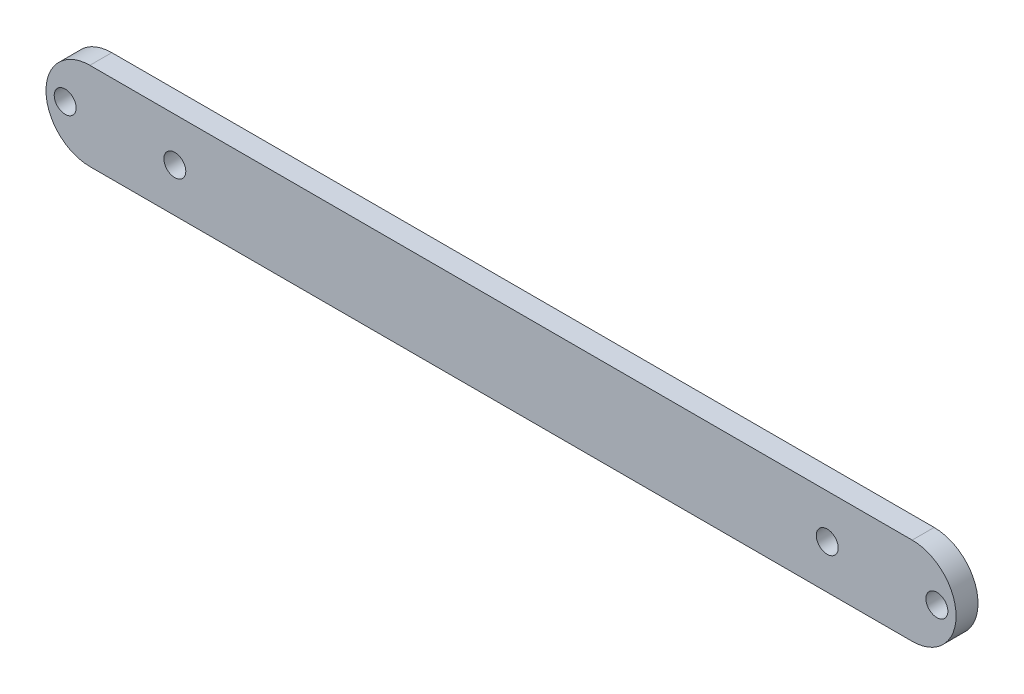
SolidWorks part; units mm, degrees
material "Thornel Mat VMA"
ref_plane "前视基准面" through (0, 0, 0) normal (0, 0, 1) x (1, 0, 0)
ref_plane "上视基准面" through (0, 0, 0) normal (0, 1, 0) x (1, 0, 0)
ref_plane "右视基准面" through (0, 0, 0) normal (1, 0, 0) x (0, 0, -1)
sketch "草图1" plane through (0, 0, 0) normal (0, 0, 1) x (1, 0, 0)
  line L0 (0, 0) -> (150, 0) construction
  line L1 (0, 8) -> (150, 8)
  line L2 (0, -8) -> (150, -8)
  arc A0 (0, 8) -> (0, -8) centre (0, 0) ccw
  arc A1 (150, -8) -> (150, 8) centre (150, 0) ccw
  circle A2 centre (0, 0) radius 2 construction
  circle A3 centre (150, 0) radius 2 construction
  point P3 (75, 0)
  dimension "D2" = 8
  dimension "D3" = 4
  dimension "D4" = 4
  dimension "D1" = 150
extrude "凸台-拉伸1" add sketch "草图1" along normal blind 4
sketch "草图2" plane through (0, 0, 4) normal (0, 0, 1) x (1, 0, 0)
  line L0 (0, 0) -> (150, 0) construction
  line L1 (-4.5, 0) -> (0, 0) construction
  line L2 (75, 8) -> (75, -38.2029) construction
  line L3 (150, 8) -> (0, 8) construction
  line L4 (150, 0) -> (150, -8) construction
  circle A0 centre (15.5, 0) radius 2
  circle A1 centre (134.5, 0) radius 2
  circle A2 centre (-4.5, 0) radius 2
  circle A3 centre (154.5, 0) radius 2
  dimension "D1" = 4
  dimension "D2" = 4
  dimension "D5" = 4
  dimension "D3" = 15.5
  dimension "D4" = 15.5
  dimension "D6" = 20
extrude "切除-拉伸1" cut sketch "草图2" against normal blind 10
